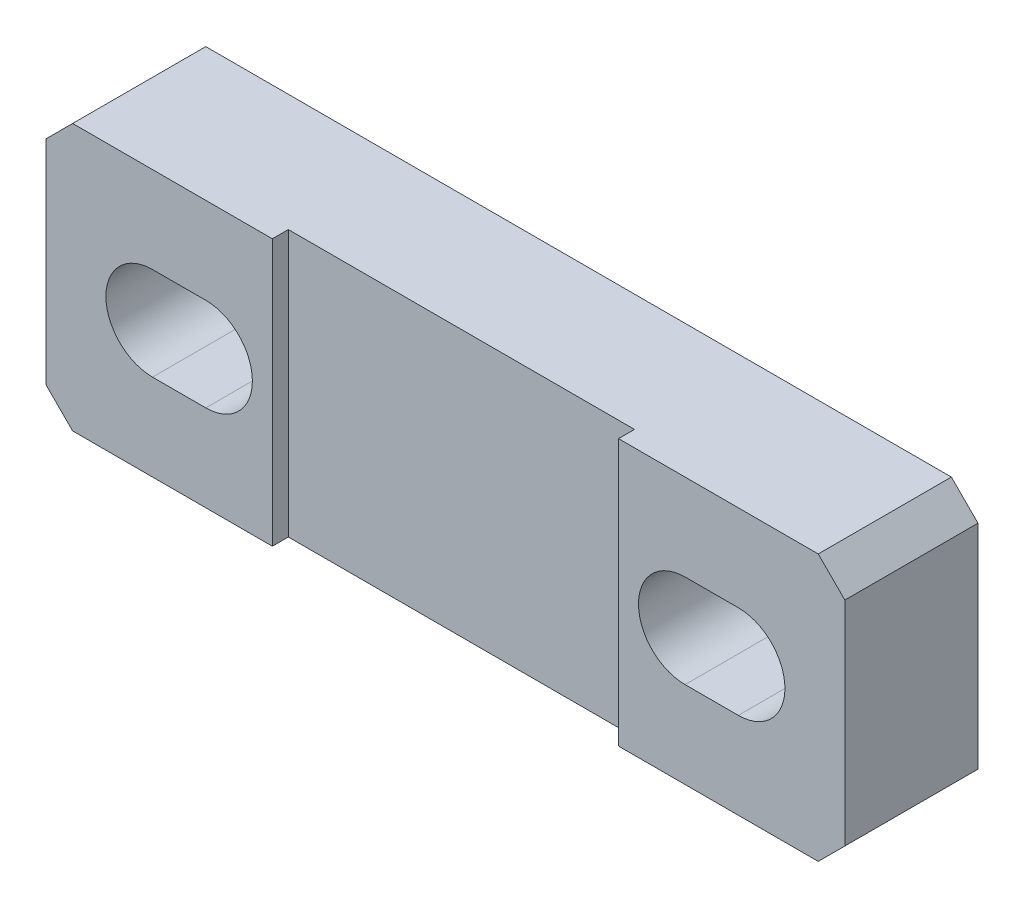
SolidWorks part; units mm, degrees
material "Lega 1060"
ref_plane "Piano frontale" through (0, 0, 0) normal (0, 0, 1) x (1, 0, 0)
ref_plane "Piano superiore" through (0, 0, 0) normal (0, 1, 0) x (1, 0, 0)
ref_plane "Piano destro" through (0, 0, 0) normal (1, 0, 0) x (0, 0, -1)
sketch "Schizzo2" plane through (0, 0, 0) normal (0, 0, 1) x (1, 0, 0)
  line L0 (0, 0) -> (-15, 0) construction
  line L1 (15, -5) -> (-15, -5)
  line L2 (15, -5) -> (15, 5)
  line L3 (15, 5) -> (-15, 5)
  line L4 (-15, -5) -> (-15, 5)
  line L5 (15, -5) -> (-15, 5) construction
  line L6 (15, 5) -> (-15, -5) construction
  line L7 (-9, 0) -> (-11, 0) construction
  line L8 (-9, -1.75) -> (-11, -1.75)
  line L9 (-9, 1.75) -> (-11, 1.75)
  line L10 (0, 0) -> (0, 5) construction
  line L11 (9, 0) -> (11, 0) construction
  line L12 (9, -1.75) -> (11, -1.75)
  line L13 (9, 1.75) -> (11, 1.75)
  arc A0 (-9, -1.75) -> (-9, 1.75) centre (-9, 0) ccw
  arc A1 (-11, 1.75) -> (-11, -1.75) centre (-11, 0) ccw
  arc A2 (9, -1.75) -> (9, 1.75) centre (9, 0) cw
  arc A3 (11, 1.75) -> (11, -1.75) centre (11, 0) cw
  point P0 (0, 0)
  point P10 (-10, 0)
  point P18 (10, 0)
  dimension "D1" = 10
  dimension "D2" = 30
  dimension "D3" = 10
  dimension "D4" = 2
  dimension "D5" = 3.5
extrude "Estrusione-Estrusione1" add sketch "Schizzo2" against normal blind 5
sketch "Schizzo3" plane through (0, 0, 0) normal (0, 0, 1) x (1, 0, 0)
  line L0 (15, 5) -> (-15, 5) construction
  line L1 (6.5, -5) -> (-6.5, -5)
  line L2 (6.5, -5) -> (6.5, 5)
  line L3 (6.5, 5) -> (-6.5, 5)
  line L4 (-6.5, -5) -> (-6.5, 5)
  line L5 (6.5, -5) -> (-6.5, 5) construction
  line L6 (6.5, 5) -> (-6.5, -5) construction
  point P0 (0, 0)
  dimension "D1" = 13
extrude "Taglio-Estrusione1" cut sketch "Schizzo3" against normal blind 0.6
chamfer "Smusso1" distance 1 angle 45 4 edges at (15, -5, -2.5) (15, 5, -2.5) (-15, -5, -2.5) (-15, 5, -2.5)
